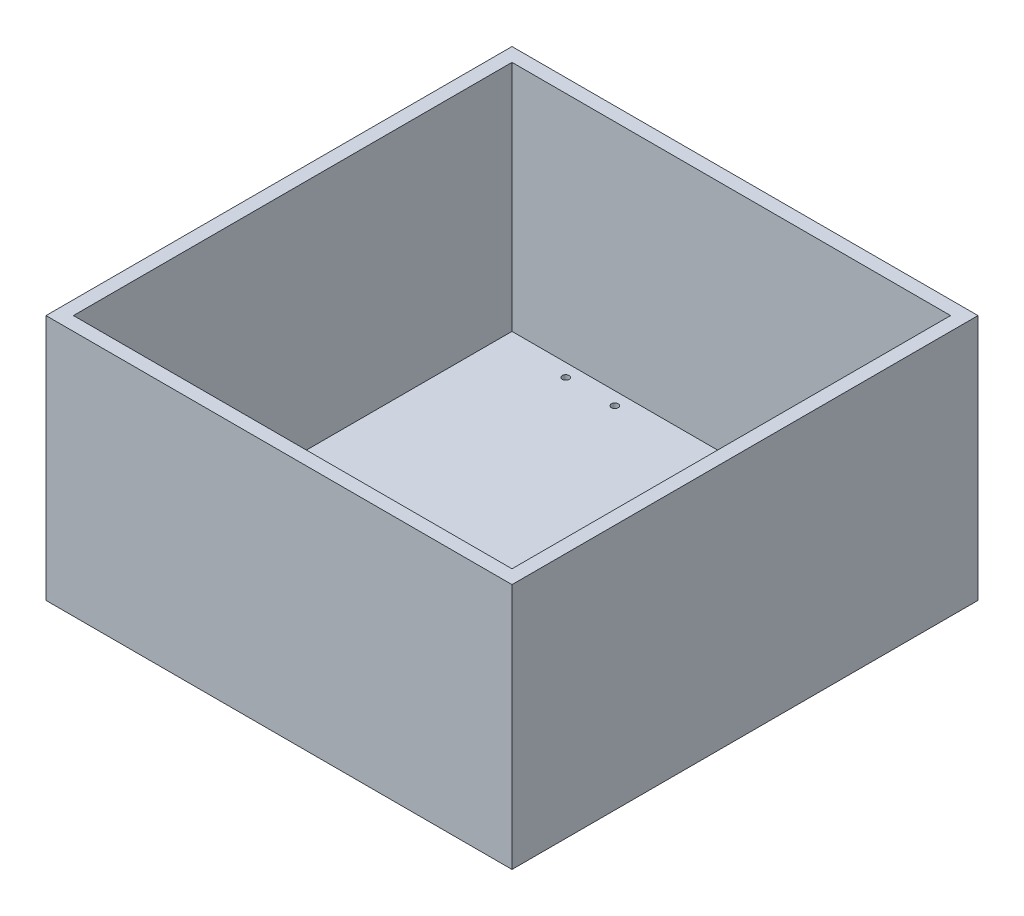
SolidWorks part; units mm, degrees
ref_plane "Front Plane" through (0, 0, 0) normal (0, 0, 1) x (1, 0, 0)
ref_plane "Top Plane" through (0, 0, 0) normal (0, 1, 0) x (1, 0, 0)
ref_plane "Right Plane" through (0, 0, 0) normal (1, 0, 0) x (0, 0, -1)
sketch "Sketch1" plane through (0, 0, 0) normal (0, 1, 0) x (1, 0, 0)
  line L1 (0, 215.9) -> (215.9, 215.9)
  line L2 (0, 215.9) -> (0, 0)
  line L3 (0, 0) -> (215.9, 0)
  line L4 (215.9, 215.9) -> (215.9, 0)
  point P4 (0, 0)
  dimension "D1" = 215.9
  dimension "D2" = 215.9
extrude "Boss-Extrude1" add sketch "Sketch1" along normal blind 114.3 contours L2 L1 L4 L3
sketch "Sketch2" plane through (0, 114.3, 0) normal (0, 1, 0) x (1, 0, 0)
  line L0 (0, 215.9) -> (215.9, 215.9) construction
  line L1 (6.35, 209.55) -> (209.55, 209.55)
  line L2 (6.35, 209.55) -> (6.35, 6.35)
  line L3 (6.35, 6.35) -> (209.55, 6.35)
  line L4 (209.55, 209.55) -> (209.55, 6.35)
  line L5 (0, 215.9) -> (0, 0) construction
  dimension "D1" = 203.2
  dimension "D2" = 203.2
  dimension "D3" = 6.35
  dimension "D4" = 6.35
extrude "Cut-Extrude1" cut sketch "Sketch2" against normal blind 107.95
sketch "Arduino Mega" plane through (0, 6.35, 0) normal (0, 1, 0) x (1, 0, 0)
  line L0 (209.55, 6.35) -> (209.55, 209.55) construction
  line L1 (196.85, 206.375) -> (118.872, 206.375)
  line L2 (196.85, 206.375) -> (196.85, 86.487)
  line L3 (196.85, 86.487) -> (118.872, 86.487)
  line L4 (118.872, 206.375) -> (118.872, 86.487)
  line L5 (209.55, 209.55) -> (6.35, 209.55) construction
  dimension "D1" = 12.7
  dimension "D2" = 3.175
  dimension "D3" = 77.978
  dimension "D4" = 119.888
sketch "Motor Driver" plane through (0, 6.35, 0) normal (0, 1, 0) x (1, 0, 0)
  line L0 (209.55, 209.55) -> (6.35, 209.55) construction
  line L1 (9.525, 206.375) -> (85.217, 206.375)
  line L2 (9.525, 206.375) -> (9.525, 88.519)
  line L3 (9.525, 88.519) -> (85.217, 88.519)
  line L4 (85.217, 206.375) -> (85.217, 88.519)
  line L5 (6.35, 209.55) -> (6.35, 6.35) construction
  line L6 (38.862, 203.5175) -> (58.42, 203.5175)
  line L7 (9.525, 147.447) -> (85.217, 147.447)
  line L8 (38.862, 91.6305) -> (58.293, 91.6305)
  circle A2 centre (37.2745, 203.5175) radius 1.5875
  circle A3 centre (60.0075, 203.5175) radius 1.5875
  circle A4 centre (59.8805, 91.6305) radius 1.5875
  circle A5 centre (37.2745, 91.6305) radius 1.5875
  point P10 (38.862, 91.6305)
  point P14 (35.687, 91.6305)
  point P17 (58.293, 91.6305)
  point P18 (60.0075, 205.105)
  point P19 (35.687, 203.5175)
  point P28 (37.2745, 90.043)
  point P29 (59.8805, 90.043)
  dimension "D5" = 19.558
  dimension "D6" = 3.175
  dimension "D7" = 3.175
  dimension "D12" = 3.175
  dimension "D13" = 3.175
  dimension "D1" = 117.856
  dimension "D2" = 75.692
  dimension "D3" = 3.175
  dimension "D4" = 3.175
  dimension "D8" = 1.27
  dimension "D9" = 26.162
  dimension "D10" = 1.524
  dimension "D11" = 19.431
  dimension "D14" = 26.162
extrude "Cut-Extrude4" cut sketch "Motor Driver" against normal blind 107.95 contours A3 | A2 | A4 | A5
sketch "Sketch6" plane through (0, 6.35, 0) normal (0, 1, 0) x (1, 0, 0)
  line L0 (6.35, 6.35) -> (209.55, 6.35) construction
  line L1 (9.525, 46.2026) -> (62.865, 46.2026)
  line L2 (9.525, 46.2026) -> (9.525, 9.525)
  line L3 (9.525, 9.525) -> (62.865, 9.525)
  line L4 (62.865, 46.2026) -> (62.865, 9.525)
  line L5 (6.35, 209.55) -> (6.35, 6.35) construction
  dimension "D1" = 36.6776
  dimension "D2" = 53.34
  dimension "D3" = 3.175
  dimension "D4" = 3.175
